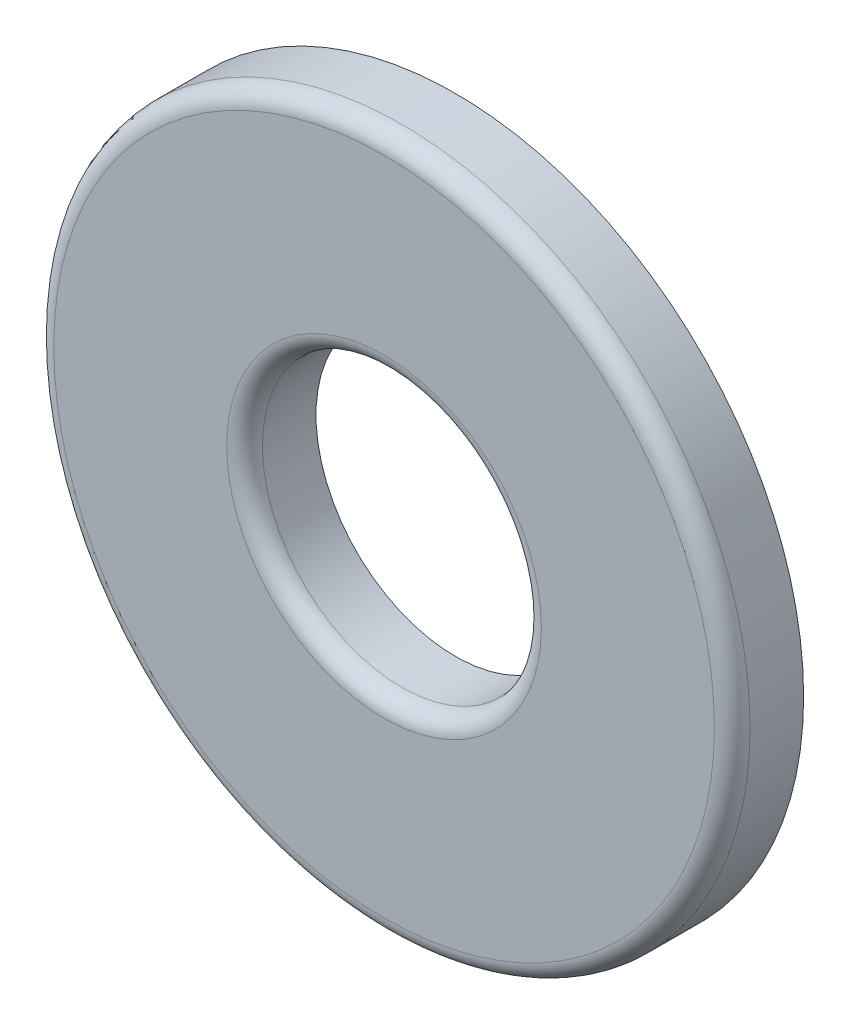
SolidWorks part; units mm, degrees
other "Imported1" parameters "D1"=0.2032, "TH"=1.0287, "Thickness"=0.8128
ref_plane "Front Plane" through (0, 0, 0) normal (0, 0, 1) x (1, 0, 0)
ref_plane "Top Plane" through (0, 0, 0) normal (0, 1, 0) x (1, 0, 0)
ref_plane "Right Plane" through (0, 0, 0) normal (1, 0, 0) x (0, 0, -1)
sketch "Sketch1" plane through (0, 0, 0) normal (0, 0, 1) x (1, 0, 0)
  line L0 (-3.9624, 0) -> (3.9624, 0) construction
  line L1 (-1.5875, 0) -> (1.5875, 0) construction
  circle A0 centre (0, 0) radius 1.5875 construction
  circle A1 centre (0, 0) radius 3.9624 construction
  point P8 (0, 0)
  point P9 (0, 3.9624)
  point P11 (1.5875, 0)
  dimension "ID" = 3.175
  dimension "OD" = 7.9248
sketch "Sketch2" plane through (0, 0, 0) normal (1, 0, 0) x (0, 0, -1)
  line L0 (-0.4064, 3.9624) -> (0.4064, 3.9624) construction
  point P2 (0, 3.9624)
sketch "Sketch3" plane through (0, 0, 0) normal (0, 0, 1) x (1, 0, 0)
  circle A0 centre (0, 0) radius 1.5875
  circle A1 centre (0, 0) radius 3.9624
extrude "Boss-Extrude1" add sketch "Sketch3" along normal up to vertex (0.4064 mm away) and the other way up to vertex (0.4064 mm away) up to point (0, 3.9624, 0.4064) other way up to point (0, 3.9624, -0.4064)
fillet "Fillet1" radius 0.2032 2 edges at (3.9624, 0, 0.4064) (1.5875, 0, 0.4064)
equation "\"D1@Fillet1\"=\"Thickness@Sketch2\"/4"
